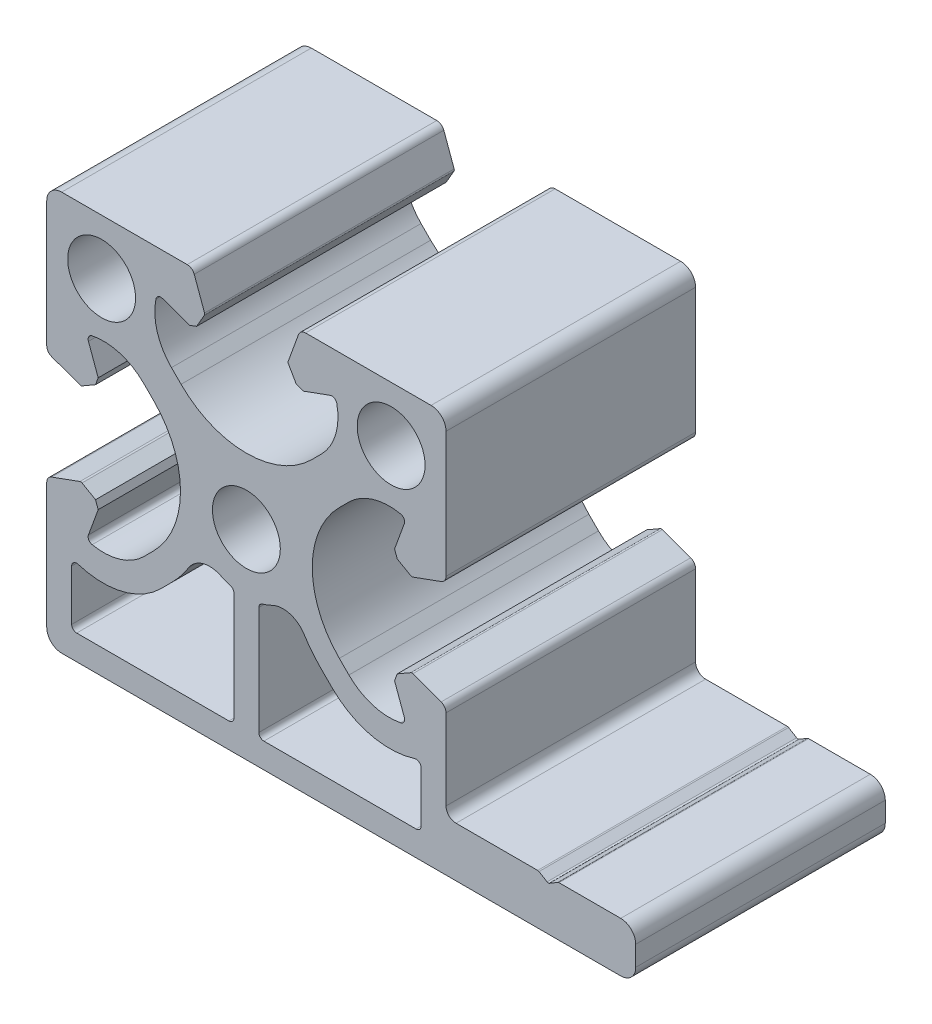
SolidWorks part; units mm, degrees
material "6005-T5"
ref_plane "Front" through (0, 0, 0) normal (0, 0, 1) x (1, 0, 0)
ref_plane "Top" through (0, 0, 0) normal (0, 1, 0) x (1, 0, 0)
ref_plane "Right" through (0, 0, 0) normal (1, 0, 0) x (0, 0, -1)
sketch "Sk Main Extrusion" plane through (0, 0, 0) normal (0, 0, 1) x (1, 0, 0)
  line L54 (-7.4415, -8.3085) -> (-8.5773, -9.4443)
  line L55 (-17.5, -11.9407) -> (-17.5, -17)
  line L56 (-17, -17.5) -> (-1.75, -17.5)
  line L57 (-1.25, -17) -> (-1.25, -6.1561)
  line L58 (1.25, -6.1561) -> (1.25, -17)
  line L59 (1.75, -17.5) -> (17, -17.5)
  line L60 (17.5, -17) -> (17.5, -11.9407)
  line L61 (8.5773, -9.4443) -> (7.4415, -8.3085)
  line L62 (-16.6712, -4.1901) -> (-19.5065, -5.2221)
  line L63 (-20, -5.9268) -> (-20, -18.5)
  line L64 (-18.5, -20) -> (37.5, -20)
  line L65 (39, -18.5) -> (39, -16.5)
  line L66 (37.5, -15) -> (31.3193, -15)
  line L67 (31.1906, -15.0357) -> (30.3788, -15.5235)
  line L68 (30.1212, -15.5235) -> (29.3094, -15.0357)
  line L69 (29.1807, -15) -> (21, -15)
  line L70 (20, -14) -> (20, -5.9268)
  line L71 (19.5065, -5.2221) -> (16.6712, -4.1901)
  line L72 (16.4607, -4.2085) -> (15.1113, -4.9876)
  line L73 (15.1113, -4.9876) -> (14.8453, -5.7185)
  line L74 (14.8453, -5.7185) -> (15.8198, -8.3962)
  line L75 (10.2727, -7.5042) -> (9.3093, -6.5407)
  line L76 (9.3093, 6.5407) -> (10.2727, 7.5042)
  line L77 (15.8198, 8.3962) -> (14.8453, 5.7185)
  line L78 (14.8453, 5.7185) -> (15.1113, 4.9876)
  line L79 (15.1113, 4.9876) -> (16.4607, 4.2085)
  line L80 (16.6712, 4.1901) -> (19.5065, 5.2221)
  line L81 (20, 5.9268) -> (20, 18.5)
  line L82 (18.5, 20) -> (5.9268, 20)
  line L83 (5.2221, 19.5065) -> (4.1901, 16.6712)
  line L84 (4.2085, 16.4607) -> (4.9876, 15.1113)
  line L85 (4.9876, 15.1113) -> (5.7185, 14.8453)
  line L86 (5.7185, 14.8453) -> (8.3962, 15.8198)
  line L87 (7.5042, 10.2727) -> (6.5407, 9.3093)
  line L88 (-6.5407, 9.3093) -> (-7.5042, 10.2727)
  line L89 (-8.3962, 15.8198) -> (-5.7185, 14.8453)
  line L90 (-5.7185, 14.8453) -> (-4.9876, 15.1113)
  line L91 (-4.9876, 15.1113) -> (-4.2085, 16.4607)
  line L92 (-4.1901, 16.6712) -> (-5.2221, 19.5065)
  line L93 (-5.9268, 20) -> (-18.5, 20)
  line L94 (-20, 18.5) -> (-20, 5.9268)
  line L95 (-19.5065, 5.2221) -> (-16.6712, 4.1901)
  line L96 (-16.4607, 4.2085) -> (-15.1113, 4.9876)
  line L97 (-15.1113, 4.9876) -> (-14.8453, 5.7185)
  line L98 (-14.8453, 5.7185) -> (-15.8198, 8.3962)
  line L99 (-10.2727, 7.5042) -> (-9.3093, 6.5407)
  line L100 (-9.3093, -6.5407) -> (-10.2727, -7.5042)
  line L101 (-15.8198, -8.3962) -> (-14.8453, -5.7185)
  line L102 (-14.8453, -5.7185) -> (-15.1113, -4.9876)
  line L103 (-15.1113, -4.9876) -> (-16.4607, -4.2085)
  circle A55 centre (14.5, 14.5) radius 3.4
  circle A56 centre (0, 0) radius 3.4
  circle A57 centre (-14.5, 14.5) radius 3.4
  arc A58 (-7.4415, -8.3085) -> (-5.7881, -6.2308) centre (-15.75, 0) ccw
  arc A59 (-16.8492, -11.464) -> (-8.5773, -9.4443) centre (-14.3755, -3.646) ccw
  arc A60 (-16.8492, -11.464) -> (-17.5, -11.9407) centre (-17, -11.9407) ccw
  arc A61 (-17.5, -17) -> (-17, -17.5) centre (-17, -17) ccw
  arc A62 (-1.75, -17.5) -> (-1.25, -17) centre (-1.75, -17) ccw
  arc A63 (-1.25, -6.1561) -> (-1.6133, -5.6751) centre (-1.75, -6.1561) ccw
  arc A64 (-2.5767, -5.3076) -> (-1.6133, -5.6751) centre (0, 0) ccw
  arc A65 (-2.5767, -5.3076) -> (-5.7881, -6.2308) centre (-3.6686, -7.5566) ccw
  arc A66 (5.7881, -6.2308) -> (2.5767, -5.3076) centre (3.6686, -7.5566) ccw
  arc A67 (1.6133, -5.6751) -> (2.5767, -5.3076) centre (0, 0) ccw
  arc A68 (1.6133, -5.6751) -> (1.25, -6.1561) centre (1.75, -6.1561) ccw
  arc A69 (1.25, -17) -> (1.75, -17.5) centre (1.75, -17) ccw
  arc A70 (17, -17.5) -> (17.5, -17) centre (17, -17) ccw
  arc A71 (17.5, -11.9407) -> (16.8492, -11.464) centre (17, -11.9407) ccw
  arc A72 (-19.5065, -5.2221) -> (-20, -5.9268) centre (-19.25, -5.9268) ccw
  arc A73 (-20, -18.5) -> (-18.5, -20) centre (-18.5, -18.5) ccw
  arc A74 (37.5, -20) -> (39, -18.5) centre (37.5, -18.5) ccw
  arc A75 (39, -16.5) -> (37.5, -15) centre (37.5, -16.5) ccw
  arc A76 (31.3193, -15) -> (31.1906, -15.0357) centre (31.3193, -15.25) ccw
  arc A77 (30.1212, -15.5235) -> (30.3788, -15.5235) centre (30.25, -15.3092) ccw
  arc A78 (29.3094, -15.0357) -> (29.1807, -15) centre (29.1807, -15.25) ccw
  arc A79 (20, -14) -> (21, -15) centre (21, -14) ccw
  arc A80 (20, -5.9268) -> (19.5065, -5.2221) centre (19.25, -5.9268) ccw
  arc A81 (16.6712, -4.1901) -> (16.4607, -4.2085) centre (16.5857, -4.425) ccw
  arc A82 (15.4507, -9.057) -> (15.8198, -8.3962) centre (15.35, -8.5672) ccw
  arc A83 (10.2727, -7.5042) -> (15.4507, -9.057) centre (14.3032, -3.4737) ccw
  arc A84 (9.3093, 6.5407) -> (9.3093, -6.5407) centre (15.85, 0) ccw
  arc A85 (15.4507, 9.057) -> (10.2727, 7.5042) centre (14.3032, 3.4737) ccw
  arc A86 (15.8198, 8.3962) -> (15.4507, 9.057) centre (15.35, 8.5672) ccw
  arc A87 (16.4607, 4.2085) -> (16.6712, 4.1901) centre (16.5857, 4.425) ccw
  arc A88 (19.5065, 5.2221) -> (20, 5.9268) centre (19.25, 5.9268) ccw
  arc A89 (20, 18.5) -> (18.5, 20) centre (18.5, 18.5) ccw
  arc A90 (5.9268, 20) -> (5.2221, 19.5065) centre (5.9268, 19.25) ccw
  arc A91 (4.1901, 16.6712) -> (4.2085, 16.4607) centre (4.425, 16.5857) ccw
  arc A92 (9.057, 15.4507) -> (8.3962, 15.8198) centre (8.5672, 15.35) ccw
  arc A93 (7.5042, 10.2727) -> (9.057, 15.4507) centre (3.4737, 14.3032) ccw
  arc A94 (-6.5407, 9.3093) -> (6.5407, 9.3093) centre (0, 15.85) ccw
  arc A95 (-9.057, 15.4507) -> (-7.5042, 10.2727) centre (-3.4737, 14.3032) ccw
  arc A96 (-8.3962, 15.8198) -> (-9.057, 15.4507) centre (-8.5672, 15.35) ccw
  arc A97 (-4.2085, 16.4607) -> (-4.1901, 16.6712) centre (-4.425, 16.5857) ccw
  arc A98 (-5.2221, 19.5065) -> (-5.9268, 20) centre (-5.9268, 19.25) ccw
  arc A99 (-18.5, 20) -> (-20, 18.5) centre (-18.5, 18.5) ccw
  arc A100 (-20, 5.9268) -> (-19.5065, 5.2221) centre (-19.25, 5.9268) ccw
  arc A101 (-16.6712, 4.1901) -> (-16.4607, 4.2085) centre (-16.5857, 4.425) ccw
  arc A102 (-15.4507, 9.057) -> (-15.8198, 8.3962) centre (-15.35, 8.5672) ccw
  arc A103 (-10.2727, 7.5042) -> (-15.4507, 9.057) centre (-14.3032, 3.4737) ccw
  arc A104 (-9.3093, -6.5407) -> (-9.3093, 6.5407) centre (-15.85, 0) ccw
  arc A105 (-15.4507, -9.057) -> (-10.2727, -7.5042) centre (-14.3032, -3.4737) ccw
  arc A106 (-15.8198, -8.3962) -> (-15.4507, -9.057) centre (-15.35, -8.5672) ccw
  arc A107 (-16.4607, -4.2085) -> (-16.6712, -4.1901) centre (-16.5857, -4.425) ccw
  arc A108 (8.5773, -9.4443) -> (16.8492, -11.464) centre (14.3755, -3.646) ccw
  arc A109 (5.7881, -6.2308) -> (7.4415, -8.3085) centre (15.75, 0) ccw
  point P109 (0, 0)
extrude "Main Extrusion" add sketch "Sk Main Extrusion" against normal blind 25
sketch "Threaded Insert Mate Sketch" plane through (0, 0, 0) normal (0, 0, 1) x (1, 0, 0)
  circle A0 centre (0, 12.7) radius 5.6515
  circle A1 centre (12.7, 0) radius 5.6515
  circle A2 centre (0, -12.7) radius 5.6515
  circle A3 centre (-12.7, 0) radius 5.6515
  point P2 (0, 0)
  point P5 (0, 0)
  point P12 (0.7677, -1.1288)
  dimension "D2" = 11.303
  dimension "D1" = 12.7
  dimension "D4" = 12.7
  dimension "D3" = 4
equation "\"Weight kg\"= round ( \"SW-Mass\" , 2 )"
equation "\"Weight lbs\"= round ( \"SW-Mass\" * 2.2046 , 2 )"
equation "\"Length mm\"= round ( \"Length@Main Extrusion\" , 2 )"
equation "\"Length in\"= round ( \"Length@Main Extrusion\" / 25.4 , 3 )"
